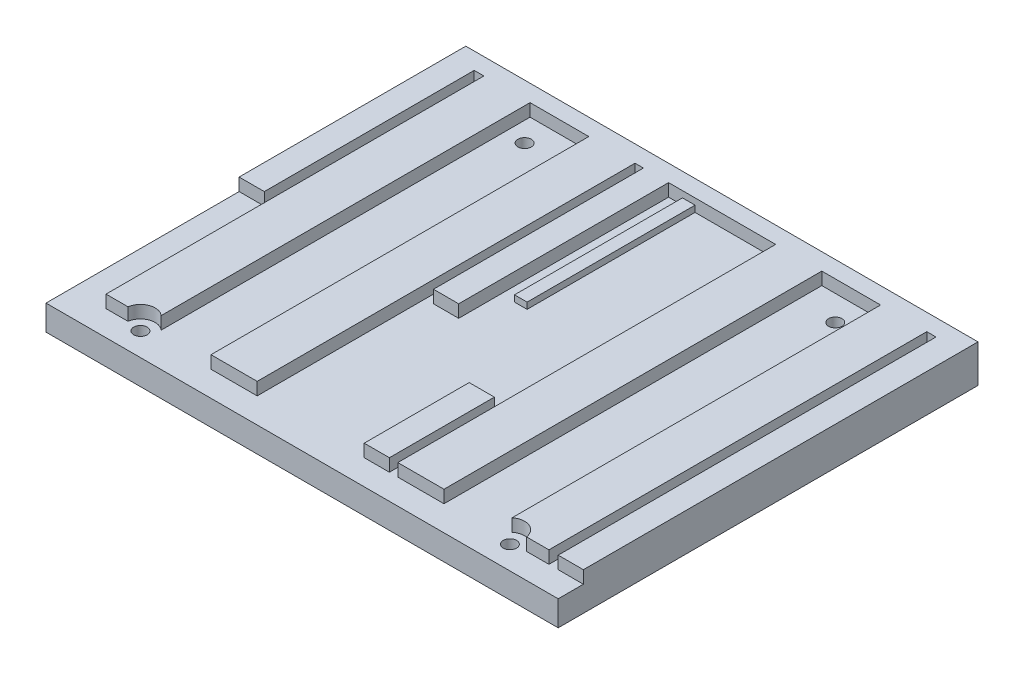
SolidWorks part; units mm, degrees
ref_plane "Front Plane" through (0, 0, 0) normal (0, 0, 1) x (1, 0, 0)
ref_plane "Top Plane" through (0, 0, 0) normal (0, 1, 0) x (1, 0, 0)
ref_plane "Right Plane" through (0, 0, 0) normal (1, 0, 0) x (0, 0, -1)
sketch "Sketch1" plane through (0, 0, 0) normal (0, 1, 0) x (1, 0, 0)
  line L1 (0, 0) -> (122, 0)
  line L2 (0, 0) -> (0, 100)
  line L3 (0, 100) -> (122, 100)
  line L4 (122, 0) -> (122, 100)
  dimension "D1" = 122
  dimension "D2" = 100
extrude "Boss-Extrude1" add sketch "Sketch1" along normal blind 3
sketch "Sketch2" plane through (0, 3, 0) normal (0, 1, 0) x (1, 0, 0)
  line L0 (0, 96) -> (122, 96) construction
  line L1 (0, 100) -> (0, 0) construction
  line L2 (122, 0) -> (122, 100) construction
  line L3 (122, 6) -> (0, 6) construction
  line L4 (122, 100) -> (0, 100) construction
  line L5 (0, 0) -> (122, 0) construction
  line L7 (0, 96) -> (6, 96)
  line L8 (0, 96) -> (0, 46)
  line L9 (0, 46) -> (6, 46)
  line L10 (6, 96) -> (6, 46)
  line L11 (8.3, 96) -> (19.3, 96)
  line L12 (8.3, 96) -> (8.3, 6)
  line L13 (8.3, 6) -> (19.3, 6)
  line L14 (19.3, 96) -> (19.3, 6)
  line L15 (33.3, 6) -> (44.3, 6)
  line L16 (33.3, 6) -> (33.3, 96)
  line L17 (33.3, 96) -> (44.3, 96)
  line L18 (44.3, 6) -> (44.3, 96)
  line L19 (46.3, 96) -> (52.3, 96)
  line L20 (46.3, 96) -> (46.3, 46)
  line L21 (46.3, 46) -> (52.3, 46)
  line L22 (52.3, 96) -> (52.3, 46)
  line L23 (69.8, 6) -> (75.8, 6)
  line L24 (69.8, 6) -> (69.8, 31)
  line L25 (69.8, 31) -> (75.8, 31)
  line L26 (75.8, 6) -> (75.8, 31)
  line L27 (77.8, 6) -> (88.8, 6)
  line L28 (77.8, 6) -> (77.8, 96)
  line L29 (77.8, 96) -> (88.8, 96)
  line L30 (88.8, 6) -> (88.8, 96)
  line L31 (102.8, 6) -> (113.8, 6)
  line L32 (102.8, 6) -> (102.8, 96)
  line L33 (102.8, 96) -> (113.8, 96)
  line L34 (113.8, 6) -> (113.8, 96)
  line L35 (116, 6) -> (122, 6)
  line L36 (116, 6) -> (116, 96)
  line L37 (116, 96) -> (122, 96)
  line L38 (122, 6) -> (122, 96)
  dimension "D1" = 4
  dimension "D2" = 6
  dimension "D3" = 6
  dimension "D4" = 2.3
  dimension "D5" = 11
  dimension "D6" = 14
  dimension "D7" = 11
  dimension "D8" = 2
  dimension "D9" = 6
  dimension "D10" = 25.5
  dimension "D11" = 6
  dimension "D12" = 25
  dimension "D13" = 2
  dimension "D14" = 11
  dimension "D15" = 14
  dimension "D16" = 11
  dimension "D17" = 6
  dimension "D18" = 50
  dimension "D19" = 50
extrude "Boss-Extrude2" add sketch "Sketch2" along normal blind 3
sketch "Sketch3" plane through (0, 3, 0) normal (0, 1, 0) x (1, 0, 0)
  line L0 (52.3, 46) -> (52.3, 96) construction
  line L1 (55.6, 96) -> (58.6, 96)
  line L2 (55.6, 96) -> (55.6, 56)
  line L3 (55.6, 56) -> (58.6, 56)
  line L4 (58.6, 96) -> (58.6, 56)
  line L5 (52.3, 96) -> (46.3, 96) construction
  dimension "D1" = 40
  dimension "D2" = 3
  dimension "D3" = 3.3
extrude "Boss-Extrude3" add sketch "Sketch3" along normal blind 1.5
sketch "Sketch4" plane through (0, 3, 0) normal (0, 1, 0) x (1, 0, 0)
  line L1 (0, 100) -> (122, 100)
  line L2 (0, 100) -> (0, 96)
  line L3 (0, 96) -> (122, 96)
  line L4 (122, 100) -> (122, 96)
extrude "Boss-Extrude4" add sketch "Sketch4" along normal blind 3
sketch "Sketch7" plane through (0, 0, 0) normal (0, -1, 0) x (1, 0, 0)
  line L4 (0, 0) -> (0, -100)
  line L5 (0, -100) -> (122, -100)
  line L6 (122, -100) -> (122, 0)
  line L7 (122, 0) -> (0, 0)
  line L8 (0, 0) -> (0, -100)
  line L9 (0, -100) -> (122, -100)
  line L10 (122, -100) -> (122, 0)
  line L11 (122, 0) -> (0, 0)
  dimension "D1" = 0
extrude "Boss-Extrude5" add sketch "Sketch7" along normal blind 3
sketch "Sketch5" plane through (0, 3, 0) normal (0, 1, 0) x (1, 0, 0)
  line L0 (0, 46) -> (0, 0) construction
  line L1 (0, 0) -> (122, 0) construction
  line L4 (0, 100) -> (0, 46) construction
  line L6 (122, 100) -> (0, 100) construction
  circle A0 centre (17, 5.5) radius 1.6
  circle A1 centre (105, 5.5) radius 1.6
  circle A2 centre (24, 90) radius 1.6
  circle A3 centre (98, 90) radius 1.6
  dimension "D1" = 17
  dimension "D2" = 3.2
  dimension "D4" = 88
  dimension "D5" = 3.2
  dimension "D6" = 5.5
  dimension "D7" = 3.2
  dimension "D8" = 3.2
  dimension "D9" = 24
  dimension "D10" = 74
  dimension "D11" = 84.5
  dimension "D3" = 5.5
  dimension "D12" = 10
extrude "standoff hole" cut sketch "Sketch5" against normal through all both and the other way through all
sketch "Sketch6" plane through (0, 3, 0) normal (0, 1, 0) x (1, 0, 0)
  circle A1 centre (17, 5.5) radius 3.5
  circle A2 centre (105, 5.5) radius 3.5
  dimension "D1" = 7
  dimension "D2" = 7
extrude "clearance hole top" cut sketch "Sketch6" along normal through all
sketch "Sketch8" plane through (0, -3, 0) normal (0, -1, 0) x (1, 0, 0)
  circle A0 centre (17, -5.5) radius 3.5
  circle A1 centre (105, -5.5) radius 3.5
  circle A2 centre (98, -90) radius 3.5
  circle A3 centre (24, -90) radius 3.5
  dimension "D1" = 7
  dimension "D2" = 7
  dimension "D3" = 7
  dimension "D4" = 7
extrude "clearance hole bottom" cut sketch "Sketch8" against normal blind 3
